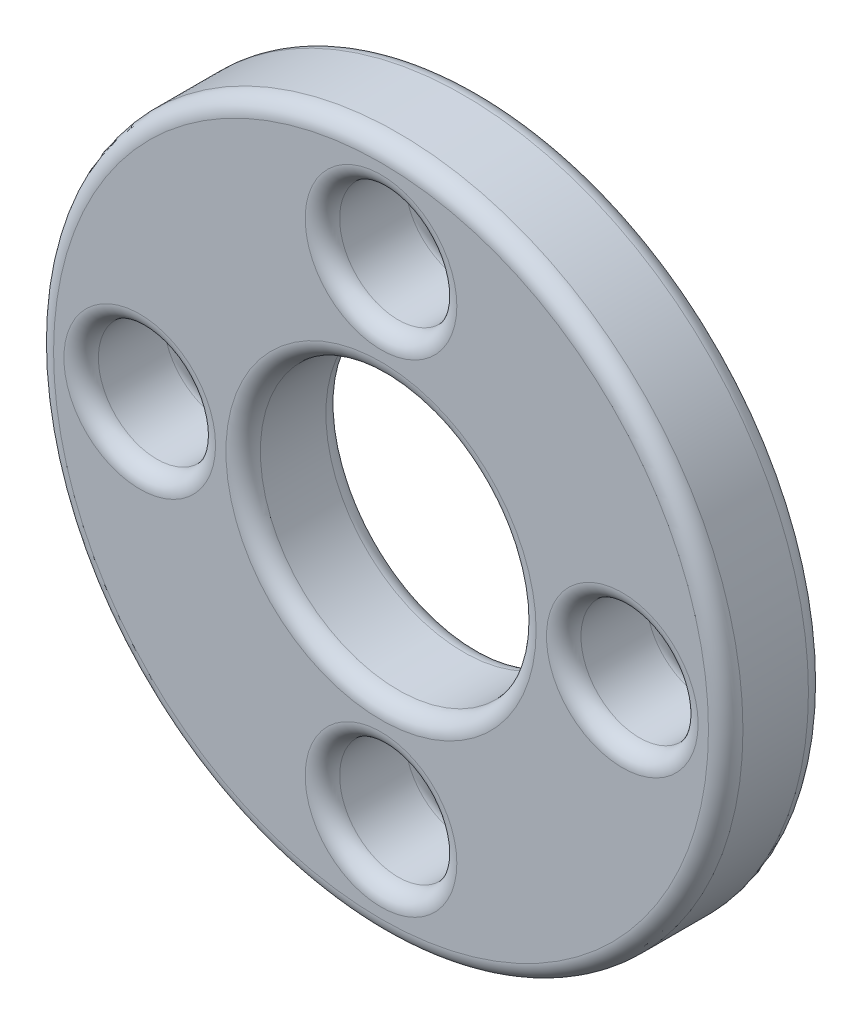
SolidWorks part; units mm, degrees
ref_plane "Front Plane" through (0, 0, 0) normal (0, 0, 1) x (1, 0, 0)
ref_plane "Top Plane" through (0, 0, 0) normal (0, 1, 0) x (1, 0, 0)
ref_plane "Right Plane" through (0, 0, 0) normal (1, 0, 0) x (0, 0, -1)
sketch "Sketch1" plane through (0, 0, 0) normal (0, 0, 1) x (1, 0, 0)
  circle A0 centre (0, 0) radius 10
  dimension "D1" = 20
extrude "Boss-Extrude1" add sketch "Sketch1" along normal blind 2.9
hole_wizard "M3 Clearance Hole1" positions "Sketch2" profile "Sketch3" hole size "M3" standard "GB" end condition through all
sketch "Sketch2" plane through (0, 0, 2.9) normal (0, 0, 1) x (1, 0, 0)
  circle A0 centre (0, 0) radius 7
  point P5 (0, 7)
  point P7 (-7, 0)
  point P9 (0, -7)
  point P11 (7, 0)
  dimension "D1" = 14
sketch "Sketch3" plane through (7, 0, 2.9) normal (1, 0, 0) x (0, -1, 0)
  line L0 (0, 0) -> (0, 2.9)
  line L1 (0, 2.9) -> (1.7, 2.9)
  line L2 (1.7, 2.9) -> (1.7, 0)
  line L5 (1.7, 0) -> (0, 0)
  line L11 (0, -6.35) -> (0, 107.95) construction
  dimension "Thru Hole Dia." = 3.4
  dimension "Thru Hole Depth" = 2.9
sketch "Sketch4" plane through (0, 0, 2.9) normal (0, 0, 1) x (1, 0, 0)
  circle A0 centre (0, 0) radius 4
  dimension "D1" = 8
extrude "Cut-Extrude1" cut sketch "Sketch4" against normal through all
fillet "Fillet1" radius 0.5 12 edges at (10, 0, 0) (8.7, 0, 0) (1.7, -7, 0) (-5.3, 0, 0) (1.7, 7, 0) (4, 0, 0) (10, 0, 2.9) (8.7, 0, 2.9) (1.7, -7, 2.9) (-5.3, 0, 2.9) (1.7, 7, 2.9) (4, 0, 2.9)
